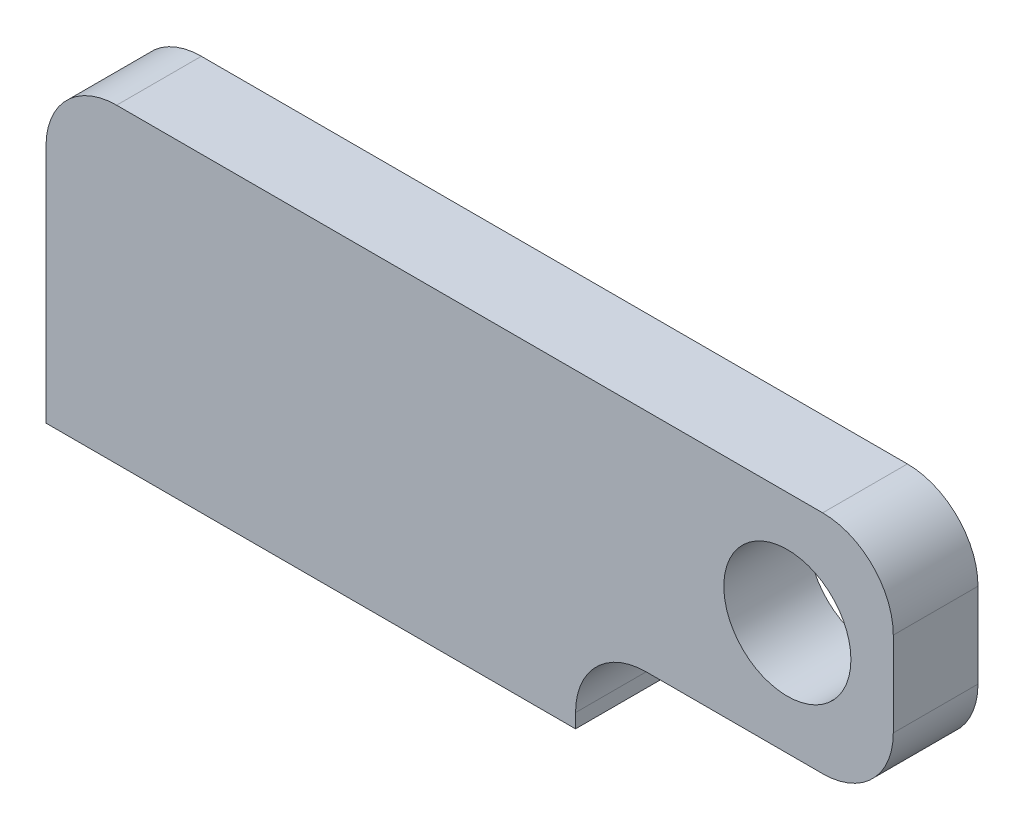
SolidWorks part; units mm, degrees
material "A3钢"
ref_plane "前视基准面" through (0, 0, 0) normal (0, 0, 1) x (1, 0, 0)
ref_plane "上视基准面" through (0, 0, 0) normal (0, 1, 0) x (1, 0, 0)
ref_plane "右视基准面" through (0, 0, 0) normal (1, 0, 0) x (0, 0, -1)
sketch "草图1" plane through (0, 0, 0) normal (0, 0, 1) x (1, 0, 0)
  line L0 (0, 0) -> (75, 0)
  line L1 (75, 0) -> (75, 12)
  line L2 (75, 12) -> (120, 12)
  line L3 (0, 0) -> (0, 44)
  line L4 (0, 44) -> (120, 44)
  line L5 (120, 44) -> (120, 12)
  dimension "D1" = 120
  dimension "D2" = 44
  dimension "D3" = 12
  dimension "D4" = 75
extrude "凸台-拉伸1" add sketch "草图1" along normal mid plane 12
hole_wizard "M6 螺纹孔1" positions "草图2" profile "草图3" tap size "M6" standard "GB"
sketch "草图2" plane through (0, 0, 0) normal (0, -1, 0) x (-1, 0, 0)
  line L0 (3.0209, 0) -> (-89.631, 0) construction
  line L3 (0, -6) -> (0, 6) construction
  point P0 (-10, 0)
  point P2 (-65, 0)
  dimension "D1" = 10
  dimension "D2" = 55
sketch "草图3" plane through (10, 0, 0) normal (1, 0, 0) x (0, 0, -1)
  line L0 (0, 0) -> (0, 19.5022)
  line L1 (0, 19.5022) -> (2.5, 18)
  line L2 (2.5, 18) -> (2.5, 0)
  line L5 (2.5, 0) -> (0, 0)
  line L10 (0, 19.5022) -> (-2.5, 18) construction
  line L11 (0, -6.35) -> (0, 107.95) construction
  dimension "螺纹孔钻头直径" = 5
  dimension "螺纹孔钻头深度" = 18
  dimension "导头角度" = 118
cosmetic thread "孔螺蚊线1" parameters "D1"=15, "D2"=6
cosmetic thread "孔螺蚊线2" parameters "D1"=15, "D2"=6
sketch "草图4" plane through (0, 0, 6) normal (0, 0, 1) x (1, 0, 0)
  line L0 (0, 0) -> (75, 0) construction
  line L1 (75, 0) -> (75, 12) construction
  circle A0 centre (105, 28) radius 9
  dimension "D2" = 18
  dimension "D1" = 28
  dimension "D3" = 30
extrude "切除-拉伸1" cut sketch "草图4" against normal through all
fillet "圆角1" radius 10 4 edges at (120, 12, 0) (120, 44, 0) (0, 44, 0) (75, 12, 0)
